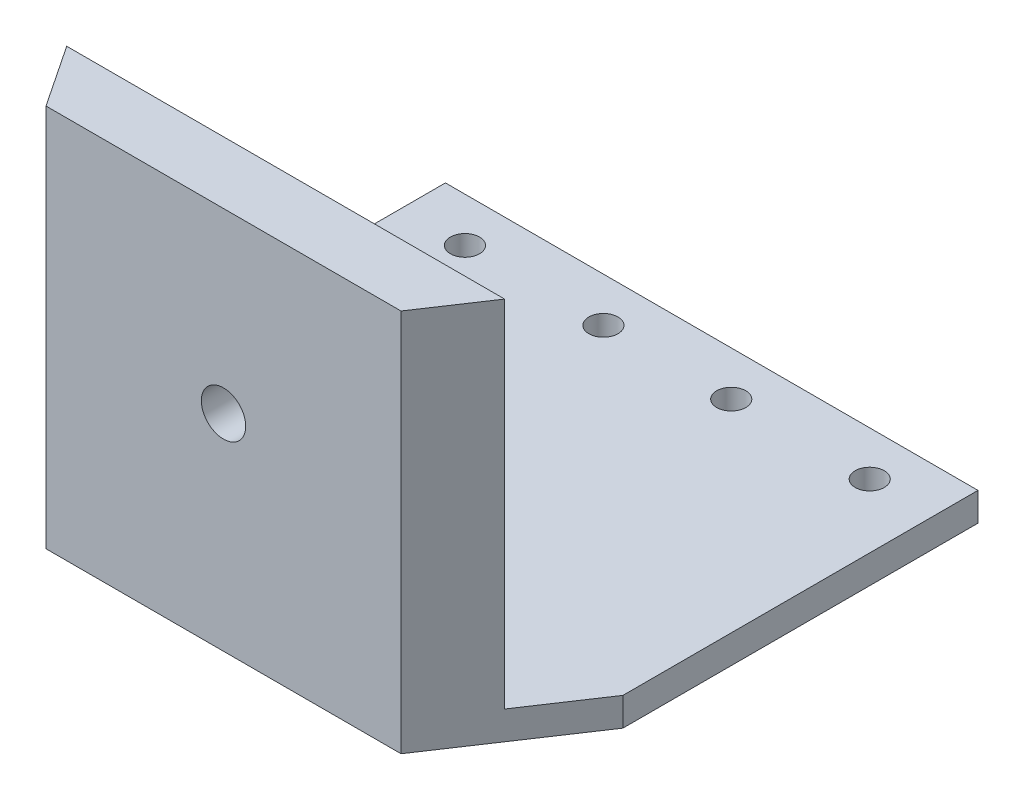
SolidWorks part; units mm, degrees
ref_plane "Front Plane" through (0, 0, 0) normal (0, 0, 1) x (1, 0, 0)
ref_plane "Top Plane" through (0, 0, 0) normal (0, 1, 0) x (1, 0, 0)
ref_plane "Right Plane" through (0, 0, 0) normal (1, 0, 0) x (0, 0, -1)
sketch "Sketch1" plane through (0, 0, 0) normal (0, 1, 0) x (1, 0, 0)
  line L0 (-38.1, -25.4) -> (-25.4, -44.45)
  line L1 (-38.1, -25.4) -> (38.1, -25.4)
  line L2 (-38.1, -25.4) -> (-38.1, 25.4)
  line L3 (-38.1, 25.4) -> (38.1, 25.4)
  line L4 (38.1, -25.4) -> (38.1, 25.4)
  line L5 (-38.1, -25.4) -> (38.1, 25.4) construction
  line L6 (-38.1, 25.4) -> (38.1, -25.4) construction
  line L7 (-25.4, -44.45) -> (25.4, -44.45)
  line L8 (25.4, -44.45) -> (38.1, -25.4)
  circle A0 centre (-28.956, 19.05) radius 2.0828
  circle A1 centre (-9.144, 19.05) radius 2.0828
  circle A2 centre (9.144, 19.05) radius 2.0828
  circle A3 centre (28.956, 19.05) radius 2.0828
  point P0 (0, 0)
  dimension "D4" = 4.1656
  dimension "D5" = 4.1656
  dimension "D6" = 4.1656
  dimension "D7" = 4.1656
  dimension "D8" = 6.35
  dimension "D9" = 9.144
  dimension "D10" = 19.812
  dimension "D11" = 9.144
  dimension "D12" = 19.812
  dimension "D1" = 76.2
  dimension "D2" = 50.8
  dimension "D3" = 50.8
extrude "Boss-Extrude1" add sketch "Sketch1" along normal mid plane 4.064 contours L1 L4 L3 L2 A3 A2 A1 A0 | L7 L8 L1 L0
sketch "Sketch2" plane through (0, 2.032, 0) normal (0, 1, 0) x (1, 0, 0)
  line L0 (-25.4, -44.45) -> (-31.3267, -35.56)
  line L1 (-38.1, -25.4) -> (-25.4, -44.45) construction
  line L2 (-31.3267, -35.56) -> (31.3267, -35.56)
  line L3 (31.3267, -35.56) -> (25.4, -44.45)
  line L4 (25.4, -44.45) -> (38.1, -25.4) construction
  line L6 (-25.4, -44.45) -> (25.4, -44.45)
  line L7 (25.4, -44.45) -> (43.2009, -76.2047)
  line M8 (-38.1, -25.4) -> (-25.4, -44.45)
  line M9 (-25.4, -44.45) -> (25.4, -44.45)
  line M10 (25.4, -44.45) -> (38.1, -25.4)
  dimension "D1" = 8.89
extrude "Boss-Extrude2" add sketch "Sketch2" along normal blind 50.8 contours L2 M8 M9 M10
sketch "Sketch3" plane through (0, 0, 35.56) normal (0, 0, -1) x (-1, 0, 0)
  line L1 (31.3267, 2.032) -> (-31.3267, 52.832)
  line L2 (-31.3267, 2.032) -> (31.3267, 52.832)
  circle A0 centre (0, 27.432) radius 3.175
  dimension "D1" = 6.35
  dimension "D2" = 0
  dimension "D3" = 0
extrude "Cut-Extrude1" cut sketch "Sketch3" against normal through all contours L2 A0 L1 | L1 A0 L2 | L2 A0 L1 | L1 A0 L2
